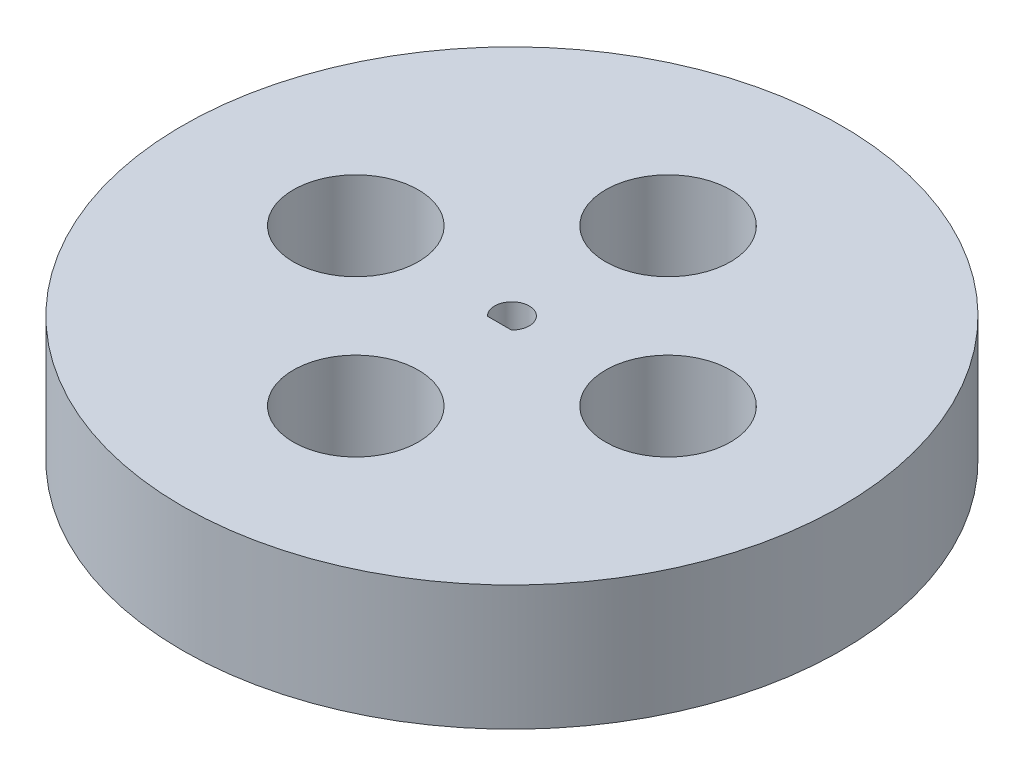
SolidWorks part; units mm, degrees
ref_plane "Front Plane" through (0, 0, 0) normal (0, 0, 1) x (1, 0, 0)
ref_plane "Top Plane" through (0, 0, 0) normal (0, 1, 0) x (1, 0, 0)
ref_plane "Right Plane" through (0, 0, 0) normal (1, 0, 0) x (0, 0, -1)
sketch "Sketch1" plane through (0, 0, 0) normal (0, 1, 0) x (1, 0, 0)
  line L0 (0, 2.7713) -> (0, -2)
  line L1 (-1.9183, -2) -> (1.9183, -2)
  arc A0 (1.9183, -2) -> (-1.9183, -2) centre (0, 0) ccw
  circle A1 centre (0, 0) radius 52.7713
  circle A2 centre (0, 0) radius 2.7713 construction
  circle A3 centre (0, 0) radius 10
  point P10 (0, -2)
  dimension "D1" = 50
  dimension "D2" = 2
extrude "Boss-Extrude1" add sketch "Sketch1" along normal blind 20 contours L1 A0 L0 | L0 A0 L1 | A1
sketch "Sketch2" plane through (0, 20, 0) normal (0, 1, 0) x (1, 0, 0)
  circle A0 centre (0, 0) radius 25
sketch "Sketch3" plane through (0, 20, 0) normal (0, 1, 0) x (1, 0, 0)
  line L0 (0, 25) -> (0, -25) construction
  line L1 (-25, 0) -> (25, 0) construction
  circle A0 centre (0, 0) radius 25 construction
  circle A1 centre (-25, 0) radius 10
  circle A2 centre (0, 25) radius 10
  circle A3 centre (25, 0) radius 10
  circle A4 centre (0, -25) radius 10
  point P8 (0, 0)
  point P12 (0, 0)
  point P19 (0, 0)
  dimension "D1" = 4
extrude "Cut-Extrude1" cut sketch "Sketch3" against normal blind 20
